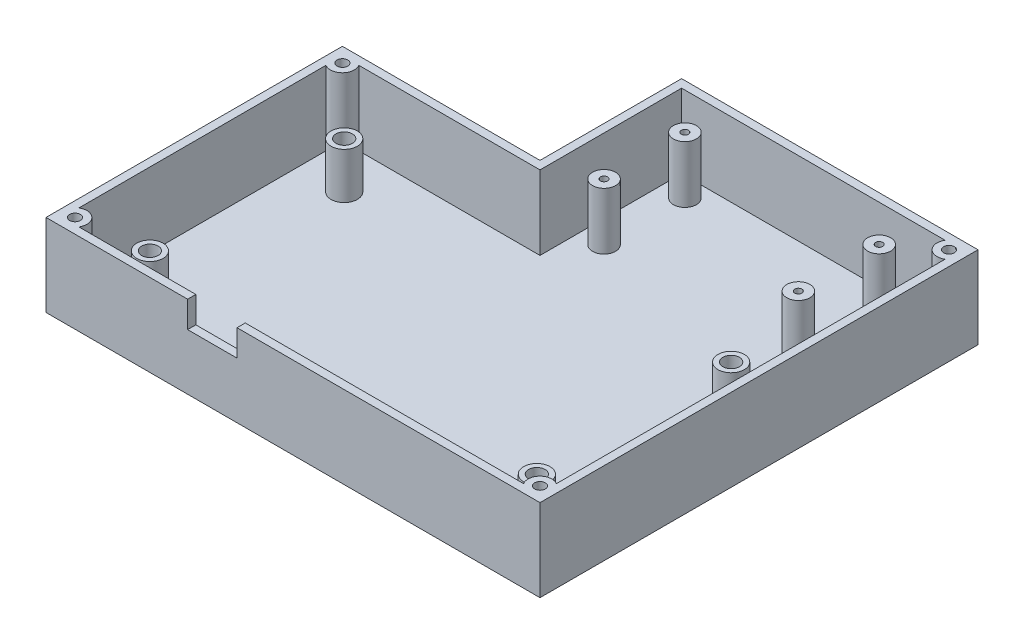
SolidWorks part; units mm, degrees
ref_plane "Front Plane" through (0, 0, 0) normal (0, 0, 1) x (1, 0, 0)
ref_plane "Top Plane" through (0, 0, 0) normal (0, 1, 0) x (1, 0, 0)
ref_plane "Right Plane" through (0, 0, 0) normal (1, 0, 0) x (0, 0, -1)
sketch "Sketch1" plane through (0, 0, 0) normal (0, 1, 0) x (1, 0, 0)
  line L1 (0, 0) -> (190.5, 0)
  line L2 (0, 0) -> (0, 114.3)
  line L3 (0, 114.3) -> (190.5, 114.3)
  line L4 (190.5, 0) -> (190.5, 114.3)
  dimension "D1" = 190.5
  dimension "D2" = 114.3
extrude "Boss-Extrude1" add sketch "Sketch1" along normal blind 31.75
sketch "Sketch2" plane through (0, 31.75, 0) normal (0, 1, 0) x (1, 0, 0)
  line L0 (0, 114.3) -> (0, 0) construction
  line L1 (3.175, 111.125) -> (187.325, 111.125)
  line L2 (3.175, 111.125) -> (3.175, 3.175)
  line L3 (3.175, 3.175) -> (187.325, 3.175)
  line L4 (187.325, 111.125) -> (187.325, 3.175)
  line L5 (190.5, 0) -> (190.5, 114.3) construction
  line L6 (0, 0) -> (190.5, 0) construction
  line L7 (190.5, 114.3) -> (0, 114.3) construction
  dimension "D1" = 3.175
  dimension "D2" = 3.175
  dimension "D3" = 3.175
  dimension "D4" = 3.175
extrude "Cut-Extrude1" cut sketch "Sketch2" against normal blind 28.575
sketch "Sketch3" plane through (0, 3.175, 0) normal (0, 1, 0) x (1, 0, 0)
  line L0 (187.325, 111.125) -> (3.175, 111.125) construction
  circle A0 centre (20.3789, 94.615) radius 5.08
  circle A1 centre (169.6039, 94.615) radius 5.08
  circle A2 centre (169.6039, 19.685) radius 5.08
  circle A3 centre (20.3789, 19.685) radius 5.08
  dimension "D1" = 10.16
  dimension "D2" = 10.16
  dimension "D3" = 10.16
  dimension "D4" = 10.16
  dimension "D5" = 74.93
  dimension "D6" = 74.93
  dimension "D7" = 149.225
  dimension "D9" = 16.51
extrude "Boss-Extrude2" add sketch "Sketch3" along normal blind 17.78
sketch "Sketch4" plane through (0, 20.955, 0) normal (0, 1, 0) x (1, 0, 0)
  circle A0 centre (20.3789, 94.615) radius 3.175
  circle A1 centre (169.6039, 94.615) radius 3.175
  circle A2 centre (20.3789, 19.685) radius 3.175
  circle A3 centre (169.6039, 19.685) radius 3.175
  dimension "D1" = 6.35
extrude "Cut-Extrude2" cut sketch "Sketch4" against normal blind 12.7
sketch "Sketch5" plane through (0, 0, 0) normal (0, 0, 1) x (1, 0, 0)
  line L1 (73.66, 21.59) -> (54.61, 21.59)
  line L2 (73.66, 21.59) -> (73.66, 46.99)
  line L3 (73.66, 46.99) -> (54.61, 46.99)
  line L4 (54.61, 21.59) -> (54.61, 46.99)
  line L5 (0, 0) -> (190.5, 0) construction
  line L6 (0, 31.75) -> (0, 0) construction
  dimension "D1" = 19.05
  dimension "D2" = 25.4
  dimension "D3" = 21.59
  dimension "D4" = 54.61
extrude "Cut-Extrude3" cut sketch "Sketch5" against normal blind 12.7
sketch "Sketch6" plane through (0, 0, 0) normal (0, -1, 0) x (1, 0, 0)
  line L1 (190.5, -114.3) -> (76.2, -114.3)
  line L2 (190.5, -114.3) -> (190.5, -168.91)
  line L3 (190.5, -168.91) -> (76.2, -168.91)
  line L4 (76.2, -114.3) -> (76.2, -168.91)
  dimension "D1" = 114.3
  dimension "D2" = 54.61
extrude "Boss-Extrude3" add sketch "Sketch6" against normal blind 31.75
sketch "Sketch7" plane through (0, 31.75, 0) normal (0, 1, 0) x (1, 0, 0)
  line L0 (76.2, 168.91) -> (190.5, 168.91) construction
  line L1 (187.325, 165.735) -> (79.375, 165.735)
  line L2 (187.325, 165.735) -> (187.325, 107.2134)
  line L3 (187.325, 107.2134) -> (79.375, 107.2134)
  line L4 (79.375, 165.735) -> (79.375, 107.2134)
  line L5 (76.2, 114.3) -> (76.2, 168.91) construction
  line L6 (190.5, 0) -> (190.5, 168.91) construction
  dimension "D1" = 3.175
  dimension "D2" = 3.175
  dimension "D3" = 3.175
extrude "Cut-Extrude4" cut sketch "Sketch7" against normal blind 28.575
sketch "Sketch8" plane through (0, 3.175, 0) normal (0, 1, 0) x (1, 0, 0)
  line L1 (76.2, 114.3) -> (76.2, 168.91) construction
  line L2 (76.2, 168.91) -> (190.5, 168.91) construction
  circle A0 centre (88.138, 127.0635) radius 4.445
  circle A1 centre (163.068, 127.0635) radius 4.445
  circle A2 centre (163.068, 158.242) radius 4.445
  circle A3 centre (88.138, 158.242) radius 4.445
  dimension "D1" = 8.89
  dimension "D2" = 74.93
  dimension "D3" = 31.1785
  dimension "D4" = 11.938
  dimension "D5" = 10.668
extrude "Boss-Extrude4" add sketch "Sketch8" along normal blind 21.971
sketch "Sketch10" plane through (0, 25.146, 0) normal (0, 1, 0) x (1, 0, 0)
  circle A0 centre (163.068, 127.0635) radius 1.3716
  circle A1 centre (88.138, 127.0635) radius 1.3716
  circle A2 centre (88.138, 158.242) radius 1.3716
  circle A3 centre (163.068, 158.242) radius 1.3716
  dimension "D1" = 2.7432
extrude "Cut-Extrude5" cut sketch "Sketch10" against normal blind 12.7
sketch "Sketch11" plane through (0, 3.175, 0) normal (0, 1, 0) x (1, 0, 0)
  line L0 (73.66, 0) -> (190.5, 0) construction
  line L1 (190.5, 0) -> (190.5, 168.91) construction
  line L2 (0, 114.3) -> (0, 0) construction
  line L3 (76.2, 114.3) -> (0, 114.3) construction
  line L4 (76.2, 168.91) -> (190.5, 168.91) construction
  circle A0 centre (184.912, 5.588) radius 4.6044
  circle A1 centre (5.588, 5.588) radius 4.6044
  circle A2 centre (5.588, 108.712) radius 4.6044
  circle A3 centre (184.912, 163.322) radius 4.6044
  point P2 (184.9852, 5.7814)
  point P5 (5.7585, 5.7814)
  point P8 (5.7585, 108.2765)
  point P11 (184.9852, 163.0951)
  point P12 (184.9852, 162.5057)
  point P19 (0, 0)
  point P20 (0, 0)
  point P21 (0, 0)
  dimension "D6" = 9.2088
  dimension "D1" = 5.588
  dimension "D2" = 5.588
  dimension "D3" = 5.588
  dimension "D4" = 5.588
  dimension "D5" = 5.588
extrude "Boss-Extrude5" add sketch "Sketch11" along normal up to surface (28.575 mm away) up to face at (83.1056, 31.75, -70.8025)
sketch "Sketch12" plane through (0, 31.75, 0) normal (0, 1, 0) x (1, 0, 0)
  circle A0 centre (184.912, 5.588) radius 2.0644
  circle A1 centre (5.588, 5.588) radius 2.0644
  circle A2 centre (5.588, 108.712) radius 2.0644
  circle A3 centre (184.912, 163.322) radius 2.0644
  arc A4 (9.5095, 3.175) -> (3.175, 9.5095) centre (5.588, 5.588) ccw construction
  arc A5 (3.175, 104.7905) -> (9.5095, 111.125) centre (5.588, 108.712) ccw construction
  arc A6 (180.9905, 165.735) -> (187.325, 159.4005) centre (184.912, 163.322) ccw construction
  arc A8 (187.325, 9.5095) -> (180.9905, 3.175) centre (184.912, 5.588) ccw construction
  arc A9 (187.325, 9.5095) -> (180.9905, 3.175) centre (184.912, 5.588) ccw construction
  point P9 (184.912, 10.1924)
  point P22 (184.912, 7.6524)
  dimension "D1" = 2.54
extrude "Cut-Extrude6" cut sketch "Sketch12" against normal up to surface (28.575 mm away) up to face at (88.138, 3.175, -153.797)
